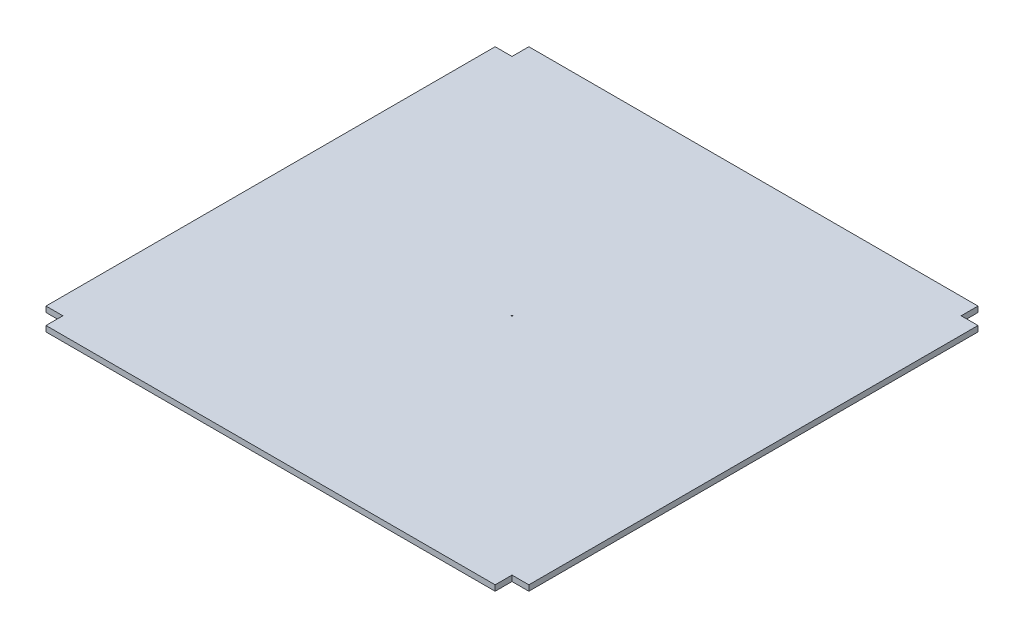
SolidWorks part; units mm, degrees
ref_plane "Front Plane" through (0, 0, 0) normal (0, 0, 1) x (1, 0, 0)
ref_plane "Top Plane" through (0, 0, 0) normal (0, 1, 0) x (1, 0, 0)
ref_plane "Right Plane" through (0, 0, 0) normal (1, 0, 0) x (0, 0, -1)
sketch "Sketch1" plane through (0, 0, 0) normal (0, 1, 0) x (1, 0, 0)
  line L0 (-430, 0) -> (430, 0) construction
  line L1 (-400, 430) -> (400, 430)
  line L2 (-430, 400) -> (-430, -400)
  line L3 (-400, -430) -> (400, -430)
  line L4 (430, 400) -> (430, -400)
  line L6 (0, 430) -> (0, -430) construction
  line L9 (-430, 400) -> (-400, 400)
  line L10 (-400, 430) -> (-400, 400)
  line L12 (-400, -430) -> (-400, -400)
  line L13 (-400, -430) -> (400, -430)
  line L14 (-430, -400) -> (-400, -400)
  line L16 (400, 430) -> (400, 400)
  line L17 (430, 400) -> (400, 400)
  line L21 (430, -400) -> (400, -400)
  line L22 (400, -430) -> (400, -400)
  line L23 (430, 400) -> (430, -400)
  point P0 (0, 0)
  point P9 (0, 0)
  dimension "D1" = 800
  dimension "D2" = 30
  dimension "D3" = 30
  dimension "D4" = 800
extrude "Boss-Extrude1" add sketch "Sketch1" along normal blind 10 contours L3 L22 L21 L4 L17 L16 L1 L10 L9 L2 L14 L12
sketch "Sketch2" plane through (0, 10, 0) normal (0, 1, 0) x (1, 0, 0)
  circle A0 centre (0, 0) radius 1
  dimension "D1" = 2
extrude "Cut-Extrude1" cut sketch "Sketch2" against normal through all both and the other way through all
